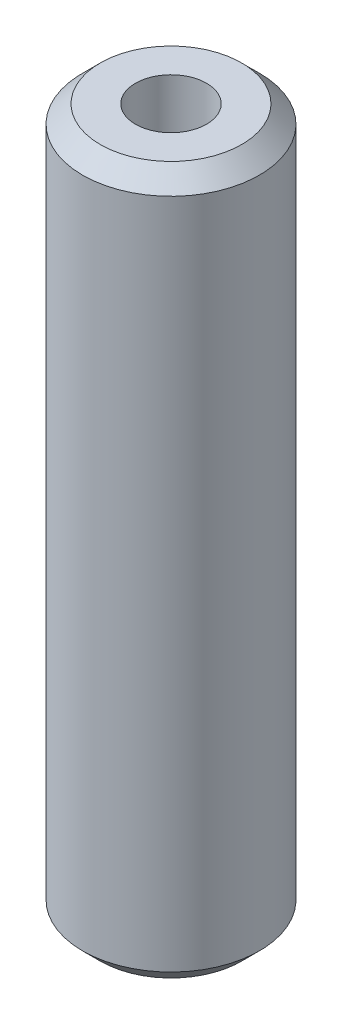
SolidWorks part; units mm, degrees
ref_plane "Front Plane" through (0, 0, 0) normal (0, 0, 1) x (1, 0, 0)
ref_plane "Top Plane" through (0, 0, 0) normal (0, 1, 0) x (1, 0, 0)
ref_plane "Right Plane" through (0, 0, 0) normal (1, 0, 0) x (0, 0, -1)
sketch "Sketch1" plane through (0, 0, 0) normal (0, 1, 0) x (1, 0, 0)
  circle A0 centre (0, 0) radius 6.35
  dimension "D1" = 12.7
extrude "Boss-Extrude1" add sketch "Sketch1" along normal blind 50.8
chamfer "Chamfer1" distance 1.27 angle 45 2 edges at (0, 0, 6.35) (0, 50.8, 6.35)
hole_wizard "1/4-20 Tapped Hole1" positions "Sketch2" profile "Sketch4" tap size "1/4-20" standard "ANSI Inch"
sketch "Sketch2" plane through (0, 0, 0) normal (0, -1, 0) x (-1, 0, 0)
  point P0 (0, 0)
sketch "Sketch4" plane through (0, 0, 0) normal (1, 0, 0) x (0, 0, -1)
  line L0 (0, 0) -> (0, 18.0438)
  line L1 (0, 18.0438) -> (2.5527, 16.51)
  line L2 (2.5527, 16.51) -> (2.5527, 0)
  line L5 (2.5527, 0) -> (0, 0)
  line L10 (0, 18.0438) -> (-2.5527, 16.51) construction
  line L11 (0, -6.35) -> (0, 107.95) construction
  dimension "Tap Drill Dia." = 5.1054
  dimension "Tap Drill Depth" = 16.51
  dimension "Drill Angle" = 118
cosmetic thread "Hole Thread1" parameters "D1"=12.7, "D2"=6.35
hole_wizard "1/4-20 Tapped Hole2" positions "Sketch5" profile "Sketch6" tap size "1/4-20" standard "ANSI Inch"
sketch "Sketch5" plane through (0, 50.8, 0) normal (0, 1, 0) x (1, 0, 0)
  point P0 (0, 0)
sketch "Sketch6" plane through (0, 50.8, 0) normal (1, 0, 0) x (0, 0, 1)
  line L0 (0, 0) -> (0, 18.0438)
  line L1 (0, 18.0438) -> (2.5527, 16.51)
  line L2 (2.5527, 16.51) -> (2.5527, 0)
  line L5 (2.5527, 0) -> (0, 0)
  line L10 (0, 18.0438) -> (-2.5527, 16.51) construction
  line L11 (0, -6.35) -> (0, 107.95) construction
  dimension "Tap Drill Dia." = 5.1054
  dimension "Tap Drill Depth" = 16.51
  dimension "Drill Angle" = 118
cosmetic thread "Hole Thread2" parameters "D1"=12.7, "D2"=6.35
